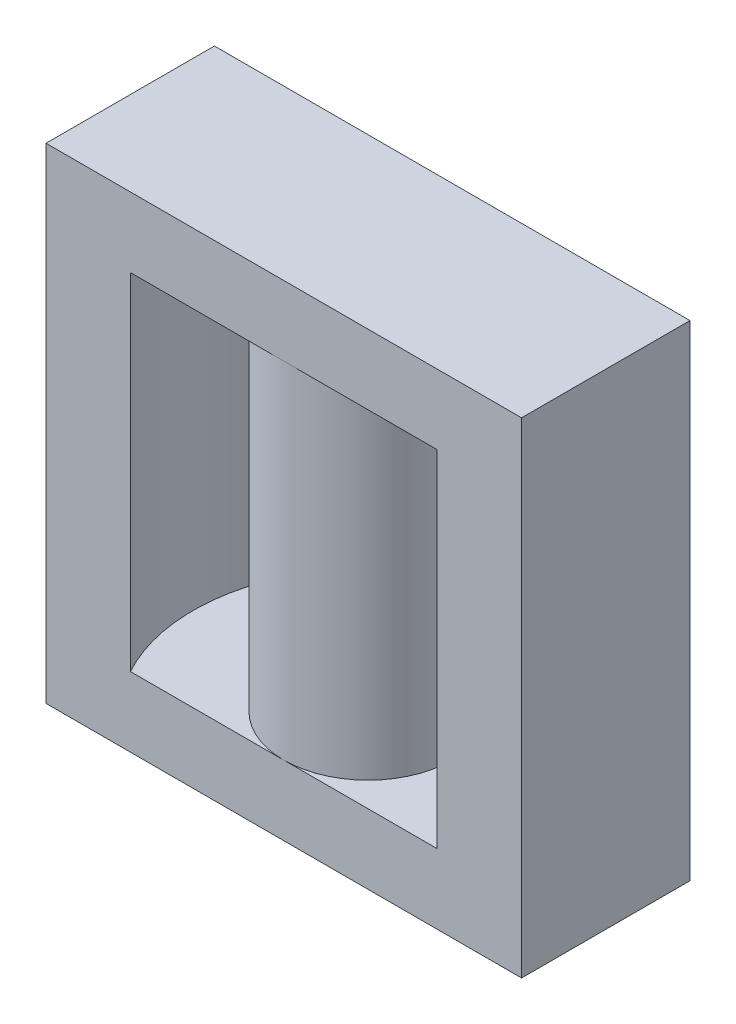
SolidWorks part; units mm, degrees
ref_plane "Front Plane" through (0, 0, 0) normal (0, 0, 1) x (1, 0, 0)
ref_plane "Top Plane" through (0, 0, 0) normal (0, 1, 0) x (1, 0, 0)
ref_plane "Right Plane" through (0, 0, 0) normal (1, 0, 0) x (0, 0, -1)
sketch "Sketch1" plane through (0, 0, 0) normal (0, 1, 0) x (1, 0, 0)
  line L1 (-27.25, 9.65) -> (27.25, 9.65)
  line L2 (-27.25, 9.65) -> (-27.25, -9.65)
  line L3 (-27.25, -9.65) -> (27.25, -9.65)
  line L4 (27.25, 9.65) -> (27.25, -9.65)
  circle A0 centre (0, 0) radius 9.65
  circle A1 centre (0, 0) radius 20.05
  dimension "D1" = 19.3
  dimension "D6" = 40.1
  dimension "D2" = 19.3
  dimension "D3" = 54.5
  dimension "D4" = 27.25
  dimension "D5" = 9.65
extrude "Boss-Extrude1" add sketch "Sketch1" along normal blind 55.6 contours A1 L1 L2 L3 | A0 | A1 L3 L4 L1
sketch "Sketch2" plane through (0, 55.6, 0) normal (0, 1, 0) x (1, 0, 0)
  line L1 (-27.25, 9.65) -> (27.25, 9.65)
  line L2 (-27.25, 9.65) -> (-27.25, -9.65)
  line L3 (-27.25, -9.65) -> (27.25, -9.65)
  line L4 (27.25, 9.65) -> (27.25, -9.65)
extrude "Boss-Extrude2" add sketch "Sketch2" against normal blind 8
sketch "Sketch3" plane through (0, 0, 0) normal (0, -1, 0) x (1, 0, 0)
  line L1 (-27.25, 9.65) -> (27.25, 9.65)
  line L2 (-27.25, 9.65) -> (-27.25, -9.65)
  line L3 (-27.25, -9.65) -> (27.25, -9.65)
  line L4 (27.25, 9.65) -> (27.25, -9.65)
extrude "Boss-Extrude3" add sketch "Sketch3" against normal blind 8
